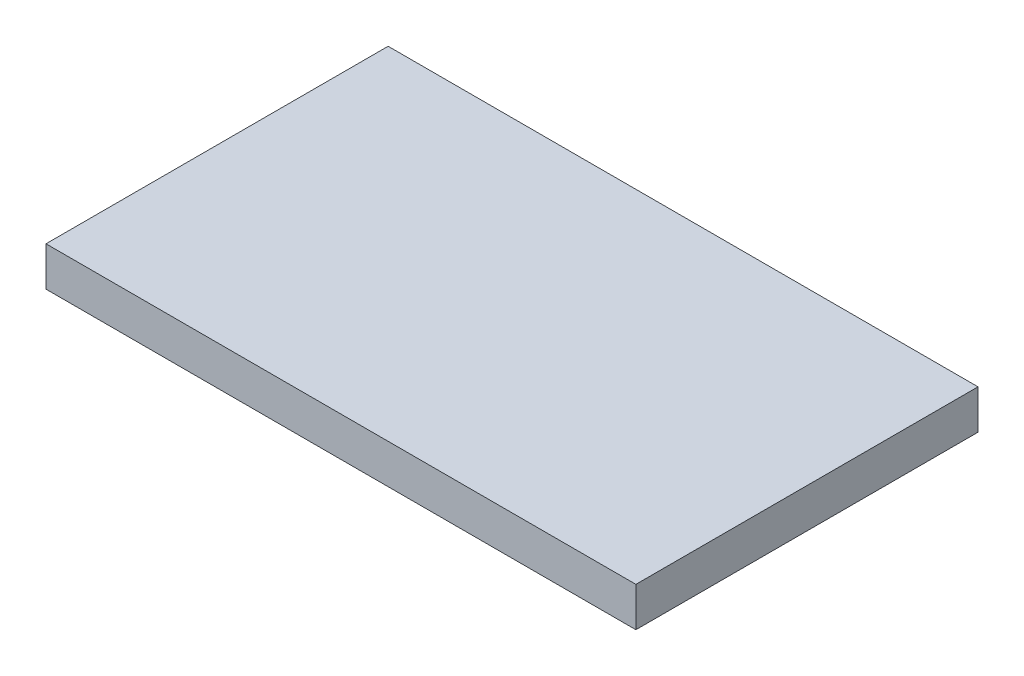
SolidWorks part; units mm, degrees
ref_plane "Front Plane" through (0, 0, 0) normal (0, 0, 1) x (1, 0, 0)
ref_plane "Top Plane" through (0, 0, 0) normal (0, 1, 0) x (1, 0, 0)
ref_plane "Right Plane" through (0, 0, 0) normal (1, 0, 0) x (0, 0, -1)
sketch "Sketch1" plane through (0, 0, 0) normal (0, 1, 0) x (1, 0, 0)
  line L1 (0, 0) -> (38.1, 0)
  line L2 (0, 0) -> (0, 22.098)
  line L3 (0, 22.098) -> (38.1, 22.098)
  line L4 (38.1, 0) -> (38.1, 22.098)
  dimension "D1" = 38.1
  dimension "D2" = 22.098
extrude "Boss-Extrude1" add sketch "Sketch1" along normal blind 2.54
